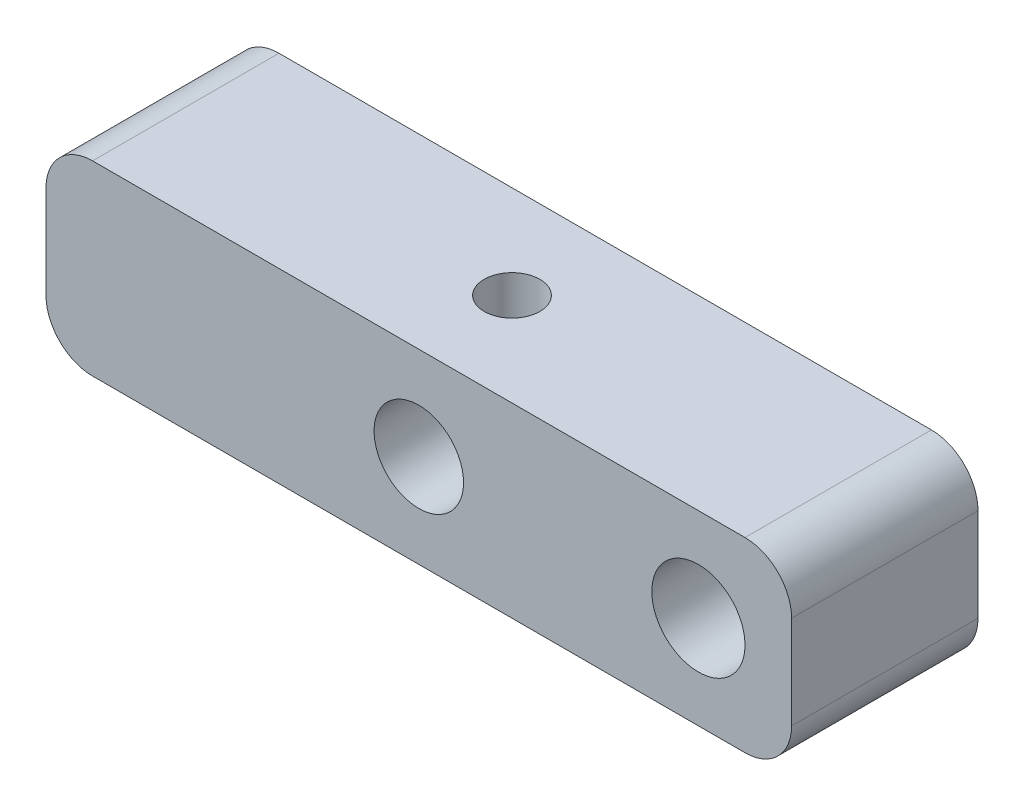
SolidWorks part; units mm, degrees
ref_plane "Front Plane" through (0, 0, 0) normal (0, 0, 1) x (1, 0, 0)
ref_plane "Top Plane" through (0, 0, 0) normal (0, 1, 0) x (1, 0, 0)
ref_plane "Right Plane" through (0, 0, 0) normal (1, 0, 0) x (0, 0, -1)
sketch "Sketch1" plane through (0, 0, 0) normal (0, 0, 1) x (1, 0, 0)
  line L1 (25.4, -6.35) -> (-25.4, -6.35)
  line L2 (25.4, -6.35) -> (25.4, 6.35)
  line L3 (25.4, 6.35) -> (-25.4, 6.35)
  line L4 (-25.4, -6.35) -> (-25.4, 6.35)
  line L5 (25.4, -6.35) -> (-25.4, 6.35) construction
  line L6 (25.4, 6.35) -> (-25.4, -6.35) construction
  point P0 (0, 0)
  dimension "D1" = 12.7
  dimension "D2" = 50.8
extrude "Boss-Extrude1" add sketch "Sketch1" along normal blind 12.7
sketch "Sketch4" plane through (0, 0, 12.7) normal (0, 0, 1) x (1, 0, 0)
  line L1 (-25.4, 6.35) -> (-25.4, -6.35) construction
  line L2 (-25.4, -6.35) -> (25.4, -6.35) construction
  circle A0 centre (0, 0) radius 3.048
  dimension "D2" = 6.096
  dimension "D1" = 25.4
  dimension "D3" = 6.35
extrude "Cut-Extrude1" cut sketch "Sketch4" against normal blind 50.8
sketch "Sketch6" plane through (0, 0, 12.7) normal (0, 0, 1) x (1, 0, 0)
  line L0 (25.4, -6.35) -> (25.4, 6.35) construction
  line L1 (25.4, 6.35) -> (-25.4, 6.35) construction
  circle A0 centre (19.05, 0) radius 3.175
  dimension "D3" = 6.35
  dimension "D1" = 6.35
  dimension "D2" = 6.35
extrude "Cut-Extrude2" cut sketch "Sketch6" against normal blind 50.8
sketch "Sketch7" plane through (0, 6.35, 0) normal (0, 1, 0) x (1, 0, 0)
  line L0 (-25.4, -12.7) -> (-25.4, 0) construction
  line L1 (25.4, -12.7) -> (-25.4, -12.7) construction
  circle A0 centre (0, -6.35) radius 2.0828
  dimension "D3" = 4.1656
  dimension "D1" = 25.4
  dimension "D2" = 6.35
hole_wizard "Tap Drill for #10-24 Tap1" positions "3DSketch1" profile "Sketch8" hole size "#10-24" standard "ANSI Inch"
sketch3d "3DSketch1"
  point P0 (0, 6.35, 6.35)
sketch "Sketch8" plane through (0, 6.35, 6.35) normal (1, 0, 0) x (0, 0, 1)
  line L0 (0, 0) -> (0, 3.302)
  line L1 (0, 3.302) -> (1.8986, 3.302)
  line L2 (1.8986, 3.302) -> (1.8986, 0)
  line L5 (1.8986, 0) -> (0, 0)
  line L11 (0, -6.35) -> (0, 107.95) construction
  dimension "Thru Hole Dia." = 3.7973
  dimension "Thru Hole Depth" = 3.302
fillet "Fillet1" radius 3.175 4 edges at (-25.4, 6.35, 6.35) (-25.4, -6.35, 6.35) (25.4, -6.35, 6.35) (25.4, 6.35, 6.35)
